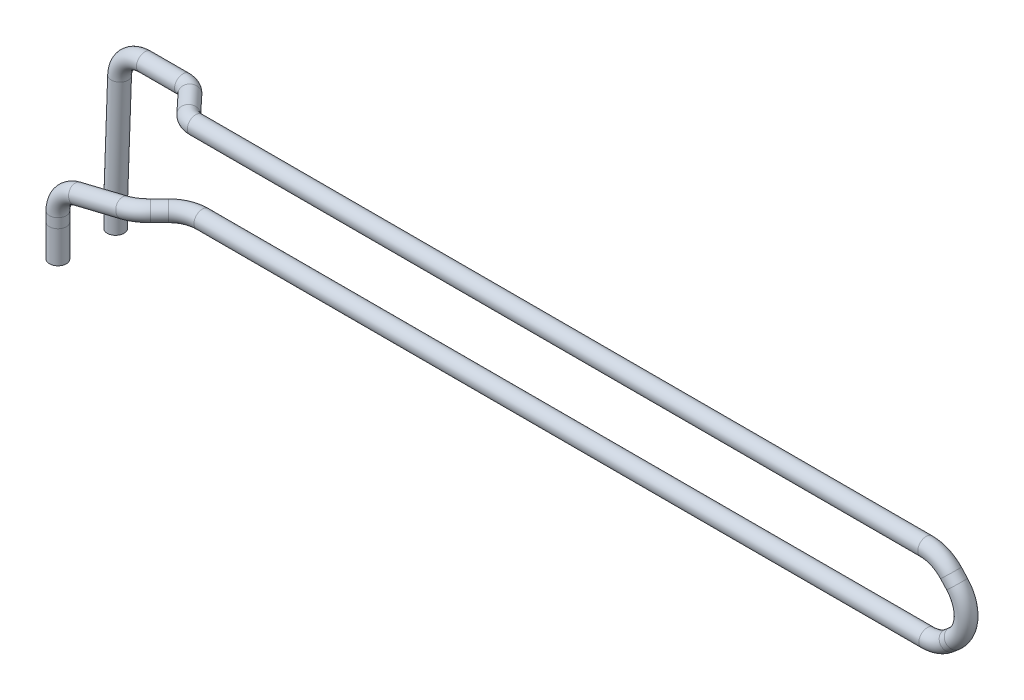
SolidWorks part; units mm, degrees
ref_plane "Front Plane" through (0, 0, 0) normal (0, 0, 1) x (1, 0, 0)
ref_plane "Top Plane" through (0, 0, 0) normal (0, 1, 0) x (1, 0, 0)
ref_plane "Right Plane" through (0, 0, 0) normal (1, 0, 0) x (0, 0, -1)
sketch3d "3DSketch1"
  line L0 (-57.8478, -11.5655, -3.1615) -> (-57.8478, -11.5655, 6.5143) construction
  line L1 (-58.0906, -9.4554, 3.4467) -> (-58.0906, -10.5909, 3.4467)
  line L3 (-48.0259, -4.8693, 2.533) -> (-46.944, -4.8693, 1.4511)
  line L4 (-44.1156, -4.8693, 0.2796) -> (41.8919, -4.8693, 0.2796)
  line L5 (44.494, -3.9073, 0.2796) -> (45.0972, -3.3906, 0.2796)
  line L6 (45.4261, 2.3694, 0.2796) -> (44.6925, 3.1593, 0.2796)
  line L7 (41.7615, 4.4372, 0.2796) -> (-44.9063, 4.4372, 0.2796)
  line L8 (-46.367, 4.4372, -0.3542) -> (-48.4, 4.4372, -2.5277)
  line L9 (-49.8606, 4.4372, -3.1615) -> (-54.3826, 4.4372, -3.1615)
  line L10 (-57.3807, 1.544, -3.1615) -> (-57.8478, -11.5655, -3.1615)
  line L11 (-50.1951, -5.1752, 3.4467) -> (-55.8006, -6.5406, 3.4467)
  line L12 (-58.0906, -10.5909, 3.4467) -> (-58.0906, -14.4017, 3.4467)
  line L13 (-57.8478, -11.5655, -3.1615) -> (-57.8478, -14.4504, -3.1615)
  arc A0 (-57.3807, 1.544, -3.1615) -> (-54.3826, 4.4372, -3.1615) centre (-54.3826, 1.4372, -3.1615) ccw
  arc A1 (-44.9063, 4.4372, 0.2796) -> (-46.367, 4.4372, -0.3542) centre (-44.9063, 4.4372, -1.7204) ccw
  arc A2 (-49.8606, 4.4372, -3.1615) -> (-48.4, 4.4372, -2.5277) centre (-49.8606, 4.4372, -1.1615) ccw
  arc A3 (-48.0259, -4.8693, 2.533) -> (-50.1951, -5.1752, 3.4467) centre (-50.0316, -5.8464, 0.5274) ccw
  arc A4 (-58.0906, -9.4554, 3.4467) -> (-55.8006, -6.5406, 3.4467) centre (-55.0906, -9.4554, 3.4467) ccw
  arc A5 (41.7615, 4.4372, 0.2796) -> (44.6925, 3.1593, 0.2796) centre (41.7615, 0.4372, 0.2796) ccw
  arc A6 (45.0972, -3.3906, 0.2796) -> (45.4261, 2.3694, 0.2796) centre (42.4951, -0.3527, 0.2796) ccw
  arc A7 (41.8919, -4.8693, 0.2796) -> (44.494, -3.9073, 0.2796) centre (41.8919, -0.8693, 0.2796) ccw
  arc A8 (-46.944, -4.8693, 1.4511) -> (-44.1156, -4.8693, 0.2796) centre (-44.1156, -4.8693, 4.2796) ccw
  point P16 (-57.2777, 4.4372, -3.1615)
  point P17 (-54.3826, 1.4372, -6.1615)
  point P20 (-45.7742, 4.4372, 0.2796)
  point P21 (-44.9063, 2.4372, -1.7204)
  point P24 (-48.9928, 4.4372, -3.1615)
  point P25 (-49.8606, 2.4372, -1.1615)
  point P27 (-48.9396, -4.8693, 3.4467)
  point P28 (-49.3406, -8.6829, 1.2183)
  point P31 (-58.0906, -7.0984, 3.4467)
  point P33 (-55.0906, -9.4554, 0.4467)
  point P36 (43.5056, 4.4372, 0.2796)
  point P37 (41.7615, 0.4372, -3.7204)
  point P40 (48.2598, -0.6818, 0.2796)
  point P41 (42.4951, -0.3527, 4.2796)
  point P44 (43.3708, -4.8693, 0.2796)
  point P45 (41.8919, -0.8693, 4.2796)
  point P48 (-45.7725, -4.8693, 0.2796)
  point P49 (-44.1156, -8.8693, 4.2796)
  dimension "D1" = 3
  dimension "D2" = 2
  dimension "D3" = 3
  dimension "D4" = 4
  dimension "D5" = 4
ref_plane "Plane1" through (-57.8478, -11.5655, -3.1615) normal (-0.0356, -0.9994, 0) x (-0.9994, 0.0356, 0)
sketch "Sketch1" plane through (-57.8478, -11.5655, -3.1615) normal (-0.0356, -0.9994, 0) x (-0.9994, 0.0356, 0)
  circle A0 centre (0, 0) radius 1
  dimension "D1" = 2
ref_plane "Plane2" through (-57.3807, 1.544, -3.1615) normal (-0.0356, -0.9994, 0) x (-0.9994, 0.0356, 0)
sketch "Sketch3" plane through (-57.3807, 1.544, -3.1615) normal (-0.0356, -0.9994, 0) x (0.9994, -0.0356, 0)
ref_plane "Plane3" through (-44.9063, 4.4372, 0.2796) normal (-1, 0, 0) x (0, 0, 1)
sweep "Sweep1" add path "3DSketch1" circular profile diameter 2 parameters "D3"=2
